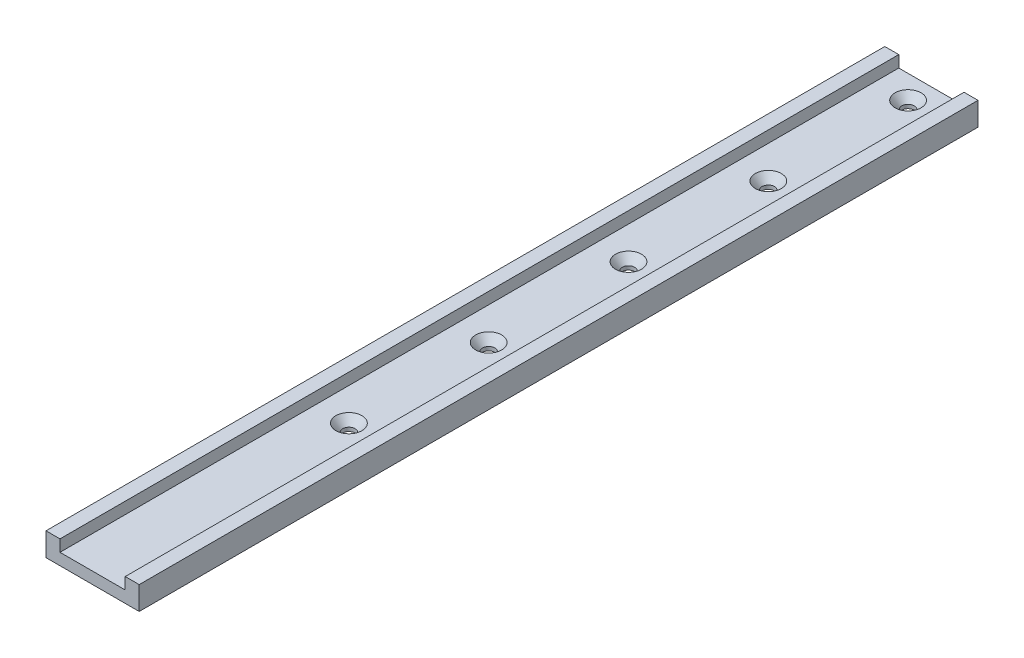
SolidWorks part; units mm, degrees
material "6061-T6 Al"
ref_plane "Front" through (0, 0, 0) normal (0, 0, 1) x (1, 0, 0)
ref_plane "Top" through (0, 0, 0) normal (0, 1, 0) x (1, 0, 0)
ref_plane "Right" through (0, 0, 0) normal (1, 0, 0) x (0, 0, -1)
sketch "Sketch" plane through (0, 0, 0) normal (0, 0, 1) x (1, 0, 0)
  line L0 (-17.78, 6.35) -> (-17.78, 12.7)
  line L2 (-25.4, 12.7) -> (-17.78, 12.7)
  line L3 (-25.4, 12.7) -> (-25.4, 0)
  line L4 (-25.4, 0) -> (25.4, 0)
  line L6 (25.4, 12.7) -> (25.4, 0)
  line L7 (-17.78, 6.35) -> (17.78, 6.35)
  line L8 (17.78, 12.7) -> (17.78, 6.35)
  line L9 (17.78, 12.7) -> (25.4, 12.7)
  point P5 (-25.908, 20.828)
  point P6 (25.908, 20.828)
  point P7 (25.908, -20.828)
  point P8 (-25.908, -20.828)
  point P38 (17.78, 12.7)
  point P63 (-25.781, -19.05)
  point P64 (25.781, -19.05)
  dimension "D3" = 35.56
  dimension "D4" = 50.8
  dimension "D1" = 12.7
  dimension "D2" = 6.35
extrude "Boss-Extrude1" add sketch "Sketch" along normal blind 457.2
hole_wizard "CSK for 1/4 Flat Head Machine Screw3" positions "Sketch5" profile "Sketch4" countersink size "1/4" standard "ANSI Inch" end condition through all
sketch "Sketch5" plane through (0, 6.35, 0) normal (0, 1, 0) x (1, 0, 0)
  line L0 (0, -12.7) -> (0, -88.9) construction
  line L1 (0, -88.9) -> (0, -165.1) construction
  line L2 (0, -165.1) -> (0, -241.3) construction
  line L3 (0, -241.3) -> (0, -317.5) construction
  line L5 (-25.4, 0) -> (25.4, 0) construction
  point P0 (0, -12.7)
  point P16 (0, -88.9)
  point P18 (0, -165.1)
  point P20 (0, -241.3)
  point P22 (0, -317.5)
  dimension "D1" = 12.7
  dimension "D2" = 76.2
sketch "Sketch4" plane through (0, 6.35, 12.7) normal (1, 0, 0) x (0, 0, 1)
  line L0 (0, 0) -> (0, 6.35)
  line L1 (0, 6.35) -> (3.3782, 6.35)
  line L2 (3.3782, 6.35) -> (3.3782, 4.2829)
  line L3 (3.3782, 4.2829) -> (7.1013, 0)
  line L5 (7.1013, 0) -> (0, 0)
  line L6 (-3.3782, 4.2829) -> (-7.1013, 0) construction
  line L11 (0, -6.35) -> (0, 107.95) construction
  dimension "Thru Hole Dia." = 6.7564
  dimension "Thru Hole Depth" = 6.35
  dimension "Near C'Sink Dia." = 14.2026
  dimension "Near C'Sink Angle" = 82
